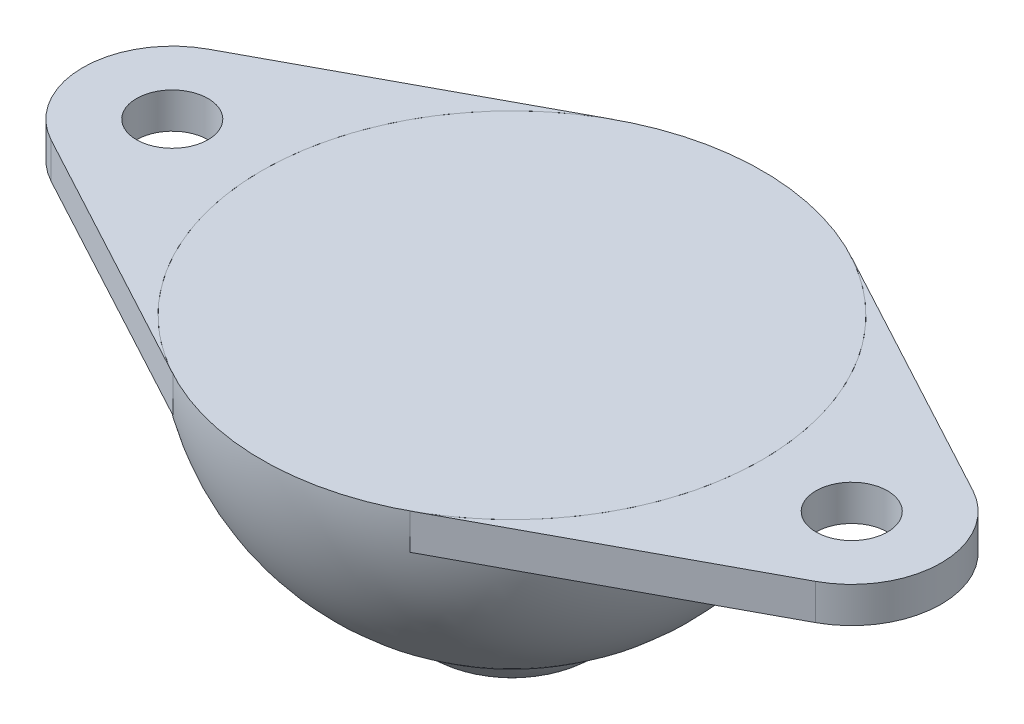
SolidWorks part; units mm, degrees
ref_plane "Front Plane" through (0, 0, 0) normal (0, 0, 1) x (1, 0, 0)
ref_plane "Top Plane" through (0, 0, 0) normal (0, 1, 0) x (1, 0, 0)
ref_plane "Right Plane" through (0, 0, 0) normal (1, 0, 0) x (0, 0, -1)
sketch "Sketch1" plane through (0, 0, 0) normal (0, 0, 1) x (1, 0, 0)
  line L0 (0, 9) -> (0, -7) construction
  line L1 (0, 9) -> (14, 9)
  line L2 (0, 9) -> (0, -7)
  line L5 (7.018, 0) -> (7.018, -3.1139)
  line L9 (7, 0) -> (7.018, 0)
  arc A2 (7.018, -3.1139) -> (14, 9) centre (0, 9) ccw
  arc A3 (0, -7) -> (7, 0) centre (0, 0) ccw
  point P4 (0, 9)
  dimension "D2" = 16
revolve "Revolve1" add sketch "Sketch1" angle 360 about L2
sketch "Sketch2" plane through (0, 9, 0) normal (0, 1, 0) x (1, 0, 0)
  line L0 (-19, 0) -> (19, 0) construction
  line L1 (0, 0) -> (0, 14) construction
  line L2 (-21.3684, 4.4035) -> (-6.6316, 12.3297)
  line L3 (-21.3684, -4.4035) -> (-6.6316, -12.3297)
  line L4 (21.3684, 4.4035) -> (6.6316, 12.3297)
  line L5 (21.3684, -4.4035) -> (6.6316, -12.3297)
  circle A1 centre (0, 0) radius 14
  circle A2 centre (-19, 0) radius 2
  circle A3 centre (-19, 0) radius 5
  circle A4 centre (19, 0) radius 2
  circle A5 centre (19, 0) radius 5
  point P3 (0, 0)
  circle M9 centre (0, 0) radius 14
  dimension "D1" = 28
  dimension "D3" = 4
  dimension "D4" = 10
  dimension "D2" = 19
extrude "Boss-Extrude1" add sketch "Sketch2" against normal blind 2 separate body contours A1 A5 L4 | L5 A5 M9 | A5 A4 | A3 L3 A1 | A3 L2 M9 | A3 A2
